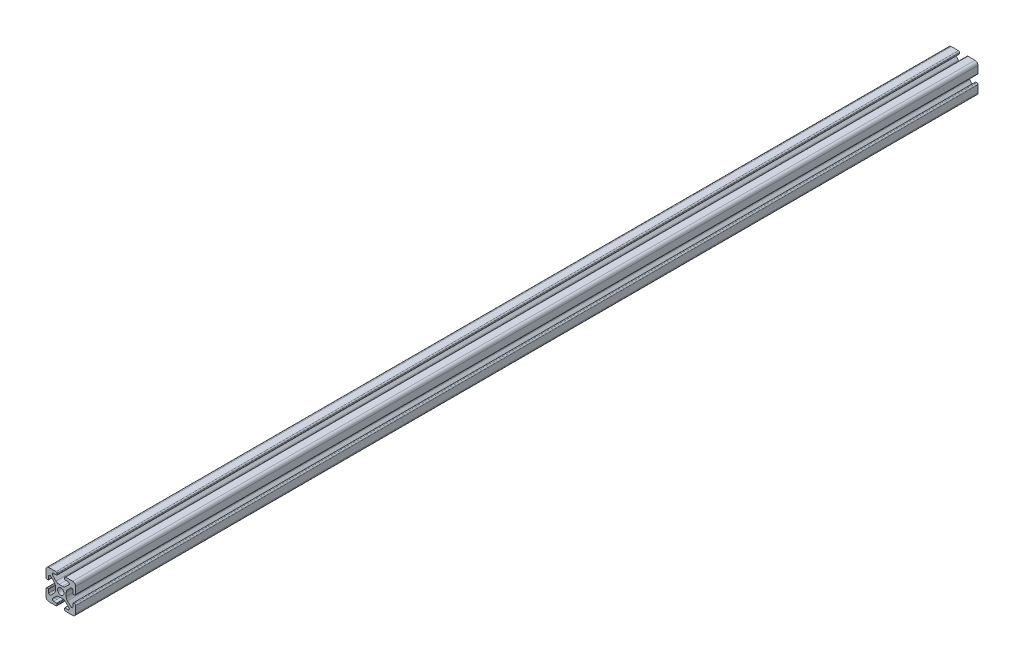
SolidWorks part; units mm, degrees
ref_plane "Front Plane" through (0, 0, 0) normal (0, 0, 1) x (1, 0, 0)
ref_plane "Top Plane" through (0, 0, 0) normal (0, 1, 0) x (1, 0, 0)
ref_plane "Right Plane" through (0, 0, 0) normal (1, 0, 0) x (0, 0, -1)
sketch "Sketch1" plane through (0, 0, 0) normal (0, 0, 1) x (1, 0, 0)
  line L0 (0, 9.9949) -> (0, -9.9949) construction
  line L1 (-9.9949, 0) -> (9.9949, 0) construction
  line L2 (-9.9949, 7.9883) -> (-9.9949, 3.2893)
  line L3 (-7.9883, 9.9949) -> (-3.2893, 9.9949)
  line L4 (-2.5019, 9.2075) -> (-2.5019, 8.4963)
  line L5 (-2.8067, 8.1915) -> (-4.9149, 8.1915)
  line L6 (-5.5076, 6.7606) -> (-3.2528, 4.5058)
  line L7 (-6.7606, 5.5076) -> (-4.5058, 3.2528)
  line L8 (-8.1915, 4.9149) -> (-8.1915, 2.8067)
  line L9 (-8.4963, 2.5019) -> (-9.2075, 2.5019)
  line L10 (0, 0) -> (-9.9949, 9.9949) construction
  line L11 (-1.1334, 3.6279) -> (1.1334, 3.6279)
  line L12 (-3.6279, 1.1334) -> (-3.6279, -1.1334)
  line L13 (8.4963, 2.5019) -> (9.2075, 2.5019)
  line L14 (8.1915, 4.9149) -> (8.1915, 2.8067)
  line L15 (9.9949, 7.9883) -> (9.9949, 3.2893)
  line L16 (7.9883, 9.9949) -> (3.2893, 9.9949)
  line L17 (2.5019, 9.2075) -> (2.5019, 8.4963)
  line L18 (2.8067, 8.1915) -> (4.9149, 8.1915)
  line L19 (3.6279, 1.1334) -> (3.6279, -1.1334)
  line L20 (5.5076, 6.7606) -> (3.2528, 4.5058)
  line L21 (6.7606, 5.5076) -> (4.5058, 3.2528)
  line L22 (-8.4963, -2.5019) -> (-9.2075, -2.5019)
  line L23 (-8.1915, -4.9149) -> (-8.1915, -2.8067)
  line L24 (-6.7606, -5.5076) -> (-4.5058, -3.2528)
  line L25 (-5.5076, -6.7606) -> (-3.2528, -4.5058)
  line L26 (-2.8067, -8.1915) -> (-4.9149, -8.1915)
  line L27 (-2.5019, -9.2075) -> (-2.5019, -8.4963)
  line L28 (-7.9883, -9.9949) -> (-3.2893, -9.9949)
  line L29 (-9.9949, -7.9883) -> (-9.9949, -3.2893)
  line L30 (9.9949, -7.9883) -> (9.9949, -3.2893)
  line L31 (7.9883, -9.9949) -> (3.2893, -9.9949)
  line L32 (2.5019, -9.2075) -> (2.5019, -8.4963)
  line L33 (2.8067, -8.1915) -> (4.9149, -8.1915)
  line L34 (5.5076, -6.7606) -> (3.2528, -4.5058)
  line L35 (6.7606, -5.5076) -> (4.5058, -3.2528)
  line L36 (8.1915, -4.9149) -> (8.1915, -2.8067)
  line L37 (8.4963, -2.5019) -> (9.2075, -2.5019)
  line L38 (-1.1334, -3.6279) -> (1.1334, -3.6279)
  circle A0 centre (0, 0) radius 2.1463
  arc A1 (-9.9949, 7.9883) -> (-7.9883, 9.9949) centre (-7.9883, 7.9883) cw
  arc A2 (-6.7606, 5.5076) -> (-8.1915, 4.9149) centre (-7.3533, 4.9149) ccw
  arc A3 (-4.9149, 8.1915) -> (-5.5076, 6.7606) centre (-4.9149, 7.3533) ccw
  arc A4 (-3.2893, 9.9949) -> (-2.5019, 9.2075) centre (-3.2893, 9.2075) cw
  arc A5 (-9.9949, 3.2893) -> (-9.2075, 2.5019) centre (-9.2075, 3.2893) ccw
  arc A6 (-8.1915, 2.8067) -> (-8.4963, 2.5019) centre (-8.4963, 2.8067) cw
  arc A7 (-2.5019, 8.4963) -> (-2.8067, 8.1915) centre (-2.8067, 8.4963) cw
  arc A8 (-1.1334, 3.6279) -> (-3.2528, 4.5058) centre (-1.1334, 6.6251) cw
  arc A9 (-3.6279, 1.1334) -> (-4.5058, 3.2528) centre (-6.6251, 1.1334) ccw
  arc A10 (8.1915, 2.8067) -> (8.4963, 2.5019) centre (8.4963, 2.8067) ccw
  arc A11 (9.9949, 3.2893) -> (9.2075, 2.5019) centre (9.2075, 3.2893) cw
  arc A12 (9.9949, 7.9883) -> (7.9883, 9.9949) centre (7.9883, 7.9883) ccw
  arc A13 (3.2893, 9.9949) -> (2.5019, 9.2075) centre (3.2893, 9.2075) ccw
  arc A14 (2.5019, 8.4963) -> (2.8067, 8.1915) centre (2.8067, 8.4963) ccw
  arc A15 (1.1334, 3.6279) -> (3.2528, 4.5058) centre (1.1334, 6.6251) ccw
  arc A16 (3.6279, 1.1334) -> (4.5058, 3.2528) centre (6.6251, 1.1334) cw
  arc A17 (6.7606, 5.5076) -> (8.1915, 4.9149) centre (7.3533, 4.9149) cw
  arc A18 (4.9149, 8.1915) -> (5.5076, 6.7606) centre (4.9149, 7.3533) cw
  arc A19 (-3.6279, -1.1334) -> (-4.5058, -3.2528) centre (-6.6251, -1.1334) cw
  arc A20 (-1.1334, -3.6279) -> (-3.2528, -4.5058) centre (-1.1334, -6.6251) ccw
  arc A21 (-2.5019, -8.4963) -> (-2.8067, -8.1915) centre (-2.8067, -8.4963) ccw
  arc A22 (-8.1915, -2.8067) -> (-8.4963, -2.5019) centre (-8.4963, -2.8067) ccw
  arc A23 (-9.9949, -3.2893) -> (-9.2075, -2.5019) centre (-9.2075, -3.2893) cw
  arc A24 (-3.2893, -9.9949) -> (-2.5019, -9.2075) centre (-3.2893, -9.2075) ccw
  arc A25 (-4.9149, -8.1915) -> (-5.5076, -6.7606) centre (-4.9149, -7.3533) cw
  arc A26 (-6.7606, -5.5076) -> (-8.1915, -4.9149) centre (-7.3533, -4.9149) cw
  arc A27 (-9.9949, -7.9883) -> (-7.9883, -9.9949) centre (-7.9883, -7.9883) ccw
  arc A28 (9.9949, -7.9883) -> (7.9883, -9.9949) centre (7.9883, -7.9883) cw
  arc A29 (6.7606, -5.5076) -> (8.1915, -4.9149) centre (7.3533, -4.9149) ccw
  arc A30 (4.9149, -8.1915) -> (5.5076, -6.7606) centre (4.9149, -7.3533) ccw
  arc A31 (3.2893, -9.9949) -> (2.5019, -9.2075) centre (3.2893, -9.2075) cw
  arc A32 (9.9949, -3.2893) -> (9.2075, -2.5019) centre (9.2075, -3.2893) ccw
  arc A33 (8.1915, -2.8067) -> (8.4963, -2.5019) centre (8.4963, -2.8067) cw
  arc A34 (2.5019, -8.4963) -> (2.8067, -8.1915) centre (2.8067, -8.4963) cw
  arc A35 (1.1334, -3.6279) -> (3.2528, -4.5058) centre (1.1334, -6.6251) cw
  arc A36 (3.6279, -1.1334) -> (4.5058, -3.2528) centre (6.6251, -1.1334) ccw
  point P29 (-9.9949, 2.5019)
  point P32 (-8.1915, 2.5019)
  point P36 (-2.3749, 3.6279)
  point P68 (0, 3.6279)
  dimension "D4" = 4.2926
  dimension "D5" = 2.0066
  dimension "D6" = 0.8382
  dimension "D9" = 0.7874
  dimension "D10" = 0.3048
  dimension "D11" = 4.7498
  dimension "D13" = 2.9972
  dimension "D1" = 19.9898
  dimension "D2" = 19.9898
  dimension "D7" = 7.493
  dimension "D8" = 1.8034
  dimension "D12" = 11.5062
extrude "Extrude1" add sketch "Sketch1" along normal mid plane 609.6
equation "\"D2@Sketch1\" = \"D1@Sketch1\""
